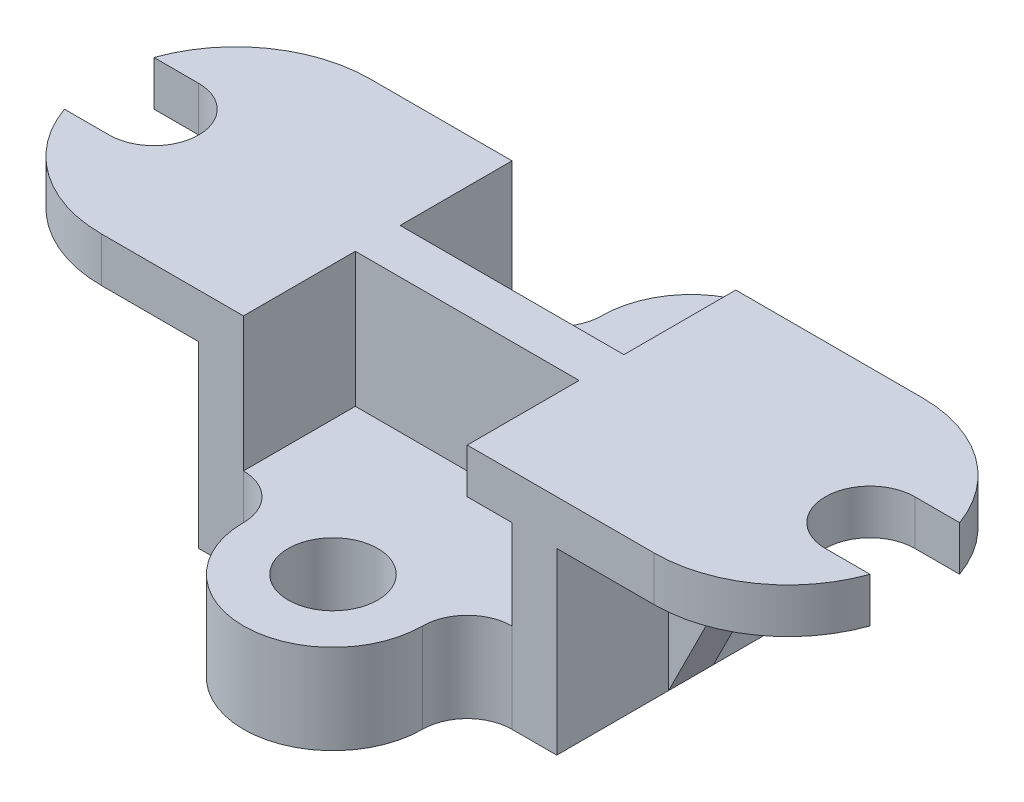
SolidWorks part; units mm, degrees
ref_plane "Front Plane" through (0, 0, 0) normal (0, 0, 1) x (1, 0, 0)
ref_plane "Top Plane" through (0, 0, 0) normal (0, 1, 0) x (1, 0, 0)
ref_plane "Right Plane" through (0, 0, 0) normal (1, 0, 0) x (0, 0, -1)
sketch "Sketch1" plane through (0, 0, 0) normal (0, 1, 0) x (1, 0, 0)
  line L1 (0, 0) -> (180, 0)
  line L2 (0, 0) -> (0, 60)
  line L3 (0, 60) -> (180, 60)
  line L4 (180, 0) -> (180, 60)
  dimension "D1" = 60
  dimension "D2" = 180
extrude "Boss-Extrude1" add sketch "Sketch1" along normal blind 10
sketch "Sketch2" plane through (0, 10, 0) normal (0, 1, 0) x (1, 0, 0)
  line L0 (0, 40) -> (10, 40)
  line L1 (0, 60) -> (0, 0) construction
  line L2 (10, 20) -> (0, 20)
  line L3 (0, 20) -> (0, 40)
  line L4 (180, 40) -> (170, 40)
  line L5 (180, 0) -> (180, 60) construction
  line L6 (170, 20) -> (180, 20)
  line L7 (180, 20) -> (180, 40)
  line L8 (180, 60) -> (0, 60) construction
  line L9 (28.2843, 60) -> (0, 60)
  line L10 (0, 60) -> (0, 40)
  line L11 (0, 0) -> (180, 0) construction
  line L12 (28.2843, 0) -> (0, 0)
  line L13 (0, 0) -> (0, 20)
  line L14 (151.7157, 60) -> (180, 60)
  line L15 (180, 60) -> (180, 0)
  line L16 (180, 0) -> (151.7157, 0)
  arc A0 (10, 40) -> (10, 20) centre (10, 30) cw
  arc A1 (170, 40) -> (170, 20) centre (170, 30) ccw
  arc A2 (0, 40) -> (28.2843, 60) centre (28.2843, 30) cw
  arc A3 (0, 20) -> (28.2843, 0) centre (28.2843, 30) ccw
  arc A4 (180, 40) -> (151.7157, 60) centre (151.7157, 30) ccw
  arc A5 (180, 20) -> (151.7157, 0) centre (151.7157, 30) cw
  line M1 (0, 60) -> (0, 0)
  line M2 (0, 0) -> (180, 0)
  line M3 (180, 0) -> (180, 60)
  line M4 (180, 60) -> (0, 60)
  dimension "D8" = 30
  dimension "D9" = 30
  dimension "D1" = 10
  dimension "D2" = 20
  dimension "D3" = 10
  dimension "D4" = 20
  dimension "D5" = 10
  dimension "D6" = 10
  dimension "D7" = 20
  dimension "D10" = 28.2843
extrude "Cut-Extrude1" cut sketch "Sketch2" against normal blind 10 contours A2 M1 M4 | A0 L0 L2 M1 | A3 M1 M2 | A5 M3 M2 | L4 A1 L6 M3 | A4 M3 M4
sketch "Sketch3" plane through (0, 0, 0) normal (0, -1, 0) x (-1, 0, 0)
  line L0 (-28.2843, 0) -> (-151.7157, 0) construction
  line L1 (-50, 0) -> (-60, 0)
  line L2 (-50, 0) -> (-50, 60)
  line L3 (-50, 60) -> (-60, 60)
  line L4 (-60, 0) -> (-60, 60)
  line L5 (-151.7157, 60) -> (-28.2843, 60) construction
  line L7 (-120, 0) -> (-130, 0)
  line L8 (-120, 0) -> (-120, 60)
  line L9 (-120, 60) -> (-130, 60)
  line L10 (-130, 0) -> (-130, 60)
  dimension "D1" = 10
  dimension "D2" = 10
  dimension "D3" = 50
  dimension "D4" = 50
extrude "Boss-Extrude2" add sketch "Sketch3" along normal blind 40
sketch "Sketch4" plane through (50, 0, 0) normal (-1, 0, 0) x (0, 0, 1)
  line L0 (0, 0) -> (-60, 0) construction
  line L1 (-35, 0) -> (-25, 0)
  line L2 (-35, 0) -> (-35, -40)
  line L3 (-35, -40) -> (-25, -40)
  line L4 (-25, 0) -> (-25, -40)
  line L5 (0, -40) -> (-60, -40) construction
  dimension "D1" = 10
  dimension "D2" = 25
extrude "Boss-Extrude3" add sketch "Sketch4" along normal blind 20
sketch "Sketch5" plane through (0, 0, -25) normal (0, 0, 1) x (1, 0, 0)
  line L0 (30, 0) -> (50, -40)
  line L1 (50, -40) -> (30, -40)
  line L2 (30, -40) -> (30, 0)
extrude "Cut-Extrude2" cut sketch "Sketch5" against normal blind 20
sketch "Sketch6" plane through (130, 0, 0) normal (1, 0, 0) x (0, 0, -1)
  line L0 (60, 0) -> (0, 0) construction
  line L1 (25, 0) -> (35, 0)
  line L2 (25, 0) -> (25, -40)
  line L3 (25, -40) -> (35, -40)
  line L4 (35, 0) -> (35, -40)
  line L5 (60, -40) -> (0, -40) construction
  dimension "D1" = 25
  dimension "D2" = 10
extrude "Boss-Extrude4" add sketch "Sketch6" along normal blind 20
sketch "Sketch7" plane through (0, 0, -25) normal (0, 0, 1) x (1, 0, 0)
  line L0 (130, -40) -> (150, 0)
  line L1 (150, 0) -> (150, -40)
  line L2 (150, -40) -> (130, -40)
extrude "Cut-Extrude3" cut sketch "Sketch7" against normal blind 20
sketch "Sketch9" plane through (0, -40, 0) normal (0, -1, 0) x (1, 0, 0)
  line L0 (60, 0) -> (60, -60)
  line L1 (120, 0) -> (120, -60)
  arc A0 (60, 0) -> (70, 10) centre (60, 10) ccw
  arc A1 (120, 0) -> (110, 10) centre (120, 10) cw
  arc A2 (110, 10) -> (70, 10) centre (90, 10) ccw
  arc A3 (60, -60) -> (70, -70) centre (60, -70) cw
  arc A4 (120, -60) -> (110, -70) centre (120, -70) ccw
  arc A5 (110, -70) -> (70, -70) centre (90, -70) cw
  dimension "D3" = 10
  dimension "D5" = 10
  dimension "D8" = 20
  dimension "D10" = 10
  dimension "D12" = 10
  dimension "D15" = 20
  dimension "D1" = 10
  dimension "D2" = 10
  dimension "D4" = 10
  dimension "D6" = 10
  dimension "D7" = 20
  dimension "D9" = 10
  dimension "D11" = 10
  dimension "D13" = 10
  dimension "D14" = 10
extrude "Boss-Extrude5" add sketch "Sketch9" against normal blind 20
sketch "Sketch10" plane through (0, -20, 0) normal (0, 1, 0) x (1, 0, 0)
  circle A0 centre (90, 70) radius 10
  circle A1 centre (90, -10) radius 10
  arc A2 (70, -10) -> (110, -10) centre (90, -10) ccw construction
  arc A3 (110, 70) -> (70, 70) centre (90, 70) ccw construction
  point P4 (90, -30)
  point P8 (90, 90)
  dimension "D1" = 20
  dimension "D2" = 20
  dimension "D3" = 20
  dimension "D4" = 0
  dimension "D5" = 20
  dimension "D6" = 20
extrude "Cut-Extrude4" cut sketch "Sketch10" against normal blind 20
sketch "Sketch11" plane through (0, 10, 0) normal (0, 1, 0) x (1, 0, 0)
  line L0 (151.7157, 60) -> (28.2843, 60) construction
  line L1 (110, 60) -> (60, 60)
  line L2 (110, 60) -> (110, 35)
  line L3 (110, 35) -> (60, 35)
  line L4 (60, 60) -> (60, 35)
  line L5 (28.2843, 0) -> (151.7157, 0) construction
  line L6 (60, 0) -> (110, 0)
  line L7 (60, 0) -> (60, 25)
  line L8 (60, 25) -> (110, 25)
  line L9 (110, 0) -> (110, 25)
  dimension "D1" = 50
  dimension "D2" = 50
  dimension "D3" = 25
  dimension "D4" = 25
  dimension "D5" = 10
  dimension "D6" = 10
extrude "Cut-Extrude5" cut sketch "Sketch11" against normal blind 20
sketch "Sketch12" plane through (0, 0, -25) normal (0, 0, 1) x (1, 0, 0)
  line L1 (60, 0) -> (120, 0)
  line L2 (60, 0) -> (60, -20)
  line L3 (60, -20) -> (120, -20)
  line L4 (120, 0) -> (120, -20)
  dimension "D1" = 0
  dimension "D2" = 0
extrude "Boss-Extrude6" add sketch "Sketch12" against normal blind 10
